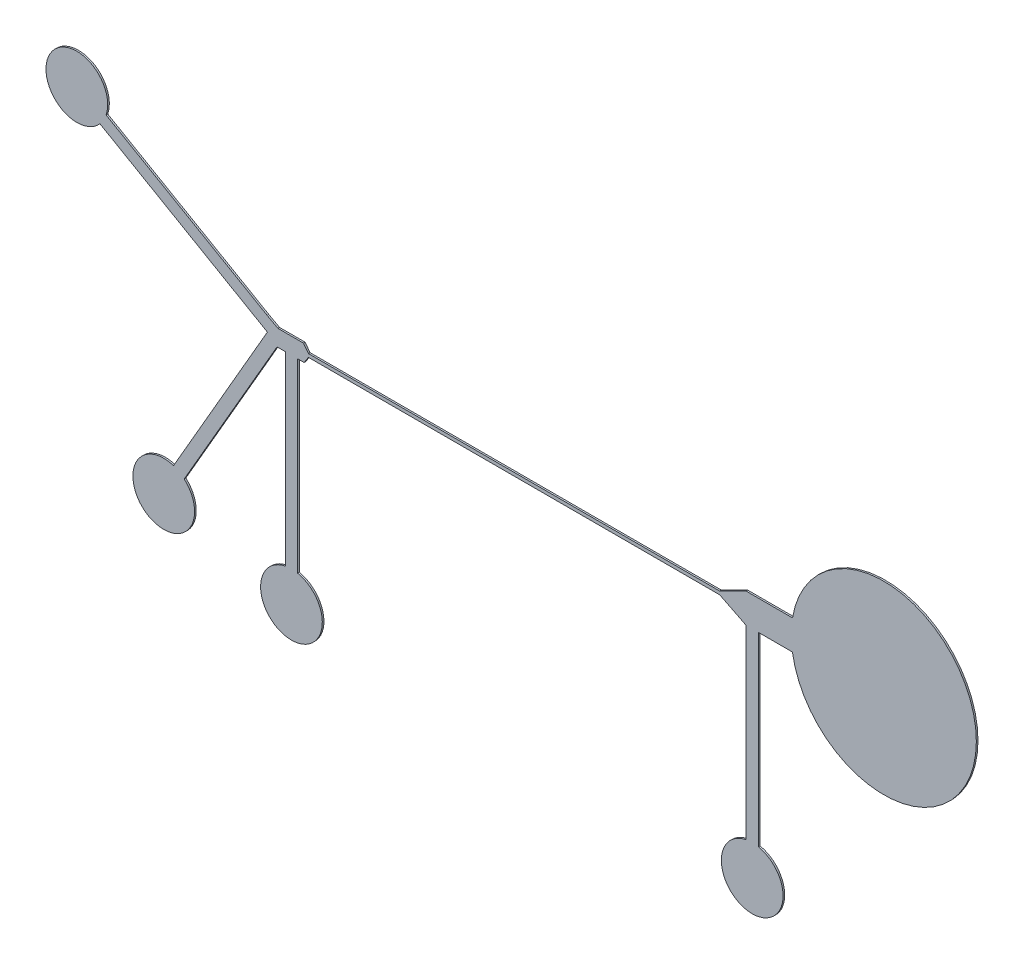
SolidWorks part; units mm, degrees
ref_plane "Front Plane" through (0, 0, 0) normal (0, 0, 1) x (1, 0, 0)
ref_plane "Top Plane" through (0, 0, 0) normal (0, 1, 0) x (1, 0, 0)
ref_plane "Right Plane" through (0, 0, 0) normal (1, 0, 0) x (0, 0, -1)
sketch "Sketch1" plane through (0, 0, 0) normal (0, 0, 1) x (1, 0, 0)
  line L18 (-1.5705, 0.1574) -> (-1.4505, -0.0026)
  line L19 (-1.4505, -0.0826) -> (-1.553, -0.2426)
  line L27 (-1.4505, -0.0026) -> (8.5495, -0.0026)
  line L28 (-1.4505, -0.0826) -> (8.5495, -0.0826)
  line L77 (-1.8505, 0.1574) -> (-1.5705, 0.1574)
  line L78 (-1.713, -0.2426) -> (-1.553, -0.2426)
  line L79 (-1.713, -0.2426) -> (-1.713, -4.7426)
  line L80 (-2.013, -0.2426) -> (-2.013, -4.7426)
  line L81 (-2.013, -4.7426) -> (-2.013, -4.7578)
  line L82 (-2.213, -0.2426) -> (-4.463, -4.1397)
  line L83 (-2.213, -0.2426) -> (-2.013, -0.2426)
  line L89 (8.5495, -0.0026) -> (9.1895, 0.3174)
  line L90 (-4.7229, -3.9897) -> (-2.4479, -0.0493)
  line L91 (-2.4479, -0.0493) -> (-6.5066, 2.294)
  line L93 (-6.3566, 2.5538) -> (-2.4594, 0.3038)
  line L94 (-1.8505, 0.1574) -> (-2.1913, 0.1574)
  line L95 (-2.4594, 0.3038) -> (-2.1913, 0.1574)
  line L96 (-1.713, -4.7426) -> (-1.713, -4.7578)
  line L97 (8.5495, -0.0826) -> (9.1895, -0.4026)
  line L98 (9.1895, -0.4026) -> (9.1895, -4.9026)
  line L99 (9.4895, -0.4026) -> (9.4895, -4.9026)
  line L100 (9.4895, -0.4026) -> (10.2895, -0.4026)
  line L101 (9.1895, 0.3174) -> (10.2895, 0.3174)
  line L102 (10.2895, 0.3174) -> (10.3196, 0.3174)
  line L103 (10.2895, -0.4026) -> (10.3174, -0.4026)
  line L104 (-6.3566, 2.5538) -> (-6.3697, 2.5614)
  line L105 (-6.5066, 2.294) -> (-6.5197, 2.3016)
  line L106 (-4.7229, -3.9897) -> (-4.7304, -4.0029)
  line L107 (-4.463, -4.1397) -> (-4.4706, -4.1529)
  line L108 (9.1895, -4.9026) -> (9.1895, -4.9178)
  line L109 (9.4895, -4.9026) -> (9.4895, -4.9178)
  arc A10 (-2.013, -4.7578) -> (-1.713, -4.7578) centre (-1.863, -5.4926) ccw
  arc A11 (-4.7304, -4.0029) -> (-4.4706, -4.1529) centre (-4.9679, -4.7143) ccw
  arc A12 (-6.3697, 2.5614) -> (-6.5197, 2.3016) centre (-7.0811, 2.7989) ccw
  arc A13 (10.3174, -0.4026) -> (10.3196, 0.3174) centre (12.5395, -0.0493) ccw
  arc A14 (9.1895, -4.9178) -> (9.4895, -4.9178) centre (9.3395, -5.6526) ccw
  point P0 (-2.013, -0.2426)
  point P2 (-1.5705, 0.1574)
  point P3 (-1.713, -0.2426)
  point P10 (-1.863, -4.7426)
  point P11 (-1.863, -4.7426)
  point P13 (-1.863, -5.4926)
  point P18 (10.2895, -0.0493)
  point P20 (-2.213, -0.2426)
  point P23 (-4.5929, -4.0647)
  point P29 (-4.9679, -4.7143)
  point P30 (12.5395, -0.0493)
  point P35 (-1.4505, -0.0826)
  point P37 (-1.5705, 0.1574)
  point P38 (-1.4505, -0.0026)
  point P39 (-1.5705, 0.1574)
  point P46 (-6.4316, 2.4239)
  point P48 (-7.0811, 2.7989)
  point P52 (9.3395, -4.9026)
  point P60 (9.3395, -5.6526)
  dimension "D7" = 0.3
  dimension "D17" = 0.32
  dimension "D23" = 2.25
  dimension "D19" = 0.64
  dimension "D14" = 0.75
  dimension "D3" = 0.16
  dimension "D4" = 0.16
  dimension "D5" = 0.64
  dimension "D6" = 0.08
  dimension "D8" = 0.16
  dimension "D9" = 4.5
  dimension "D10" = 0.15
  dimension "D11" = 0.75
  dimension "D12" = 10
  dimension "D13" = 0.2
  dimension "D15" = 0.75
  dimension "D16" = 0.12
  dimension "D18" = 0.32
  dimension "D20" = 0.08
  dimension "D21" = 0.3
  dimension "D22" = 0.8
  dimension "D24" = 0.15
  dimension "D25" = 0.75
extrude "Boss-Extrude1" add sketch "Sketch1" along normal blind 0.04
